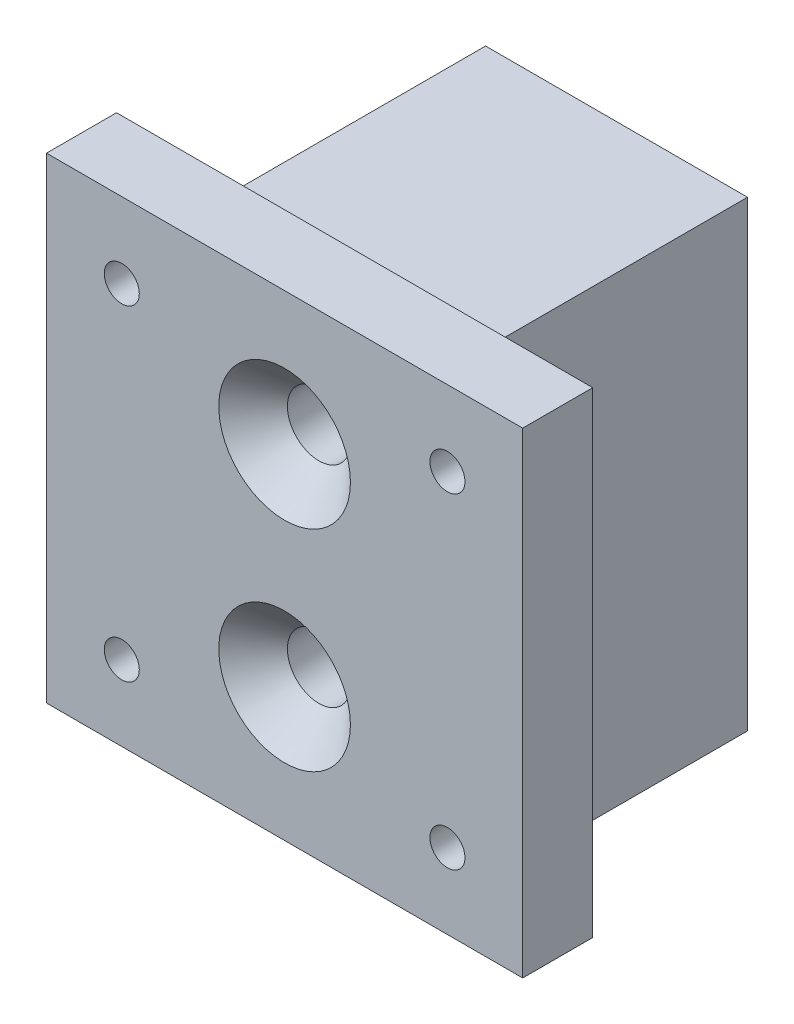
SolidWorks part; units mm, degrees
ref_plane "Front Plane" through (0, 0, 0) normal (0, 0, 1) x (1, 0, 0)
ref_plane "Top Plane" through (0, 0, 0) normal (0, 1, 0) x (1, 0, 0)
ref_plane "Right Plane" through (0, 0, 0) normal (1, 0, 0) x (0, 0, -1)
sketch "Sketch3" plane through (0, 0, 0) normal (0, 1, 0) x (1, 0, 0)
  line L1 (3, 3) -> (15.7, 3)
  line L2 (3, 3) -> (3, 15.7)
  line L3 (3, 15.7) -> (15.7, 15.7)
  line L4 (15.7, 3) -> (15.7, 15.7)
  line L5 (18.7, 18.7) -> (0, 18.7)
  line L6 (18.7, 18.7) -> (18.7, 0)
  line L7 (18.7, 0) -> (0, 0)
  line L8 (0, 18.7) -> (0, 0)
  dimension "D1" = 12.7
  dimension "D2" = 12.7
  dimension "D3" = 3
  dimension "D4" = 3
  dimension "D5" = 3
  dimension "D6" = 3
extrude "Boss-Extrude2" add sketch "Sketch3" along normal blind 30
sketch "Sketch4" plane through (0, 30, 0) normal (0, 1, 0) x (1, 0, 0)
  line L1 (0, 18.7) -> (18.7, 18.7)
  line L2 (0, 18.7) -> (0, 0)
  line L3 (0, 0) -> (18.7, 0)
  line L4 (18.7, 18.7) -> (18.7, 0)
extrude "Boss-Extrude3" add sketch "Sketch4" along normal blind 3
sketch "Sketch7" plane through (0, 0, 0) normal (0, 0, 1) x (1, 0, 0)
  line L1 (18.7, 33) -> (18.7, 0) construction
  line L2 (0, 33) -> (18.7, 33) construction
  point P0 (9.35, 24.9)
  point P1 (9.35, 9.9)
sketch "Sketch9" plane through (0, 0, 0) normal (0, 0, 1) x (1, 0, 0)
  line L0 (18.7, 33) -> (18.7, 0) construction
  line L1 (-7.65, 34.4) -> (26.35, 34.4)
  line L2 (-7.65, 34.4) -> (-7.65, 0.4)
  line L3 (-7.65, 0.4) -> (26.35, 0.4)
  line L4 (26.35, 34.4) -> (26.35, 0.4)
  point P4 (9.35, 17.4)
  point P5 (9.35, 17.4)
  dimension "D1" = 34
  dimension "D2" = 34
  dimension "D3" = 17
  dimension "D4" = 17
extrude "Boss-Extrude4" add sketch "Sketch9" along normal blind 5
sketch "Sketch10" plane through (0, 0, 5) normal (0, 0, 1) x (1, 0, 0)
  point P0 (9.35, 24.9)
  point P1 (9.35, 9.9)
hole_wizard "CSK for M4 Flat Head Machine Screw3" positions "3DSketch4" profile "Sketch11" countersink size "M4" standard "ANSI Metric" end condition through all
sketch3d "3DSketch4"
  point P0 (9.35, 24.9, 5)
  point P3 (9.35, 9.9, 5)
sketch "Sketch11" plane through (9.35, 24.9, 5) normal (1, 0, 0) x (0, -1, 0)
  line L0 (0, 0) -> (0, 23.7)
  line L1 (0, 23.7) -> (2.25, 23.7)
  line L2 (2.25, 23.7) -> (2.25, 2.45)
  line L3 (2.25, 2.45) -> (4.7, 0)
  line L5 (4.7, 0) -> (0, 0)
  line L6 (-2.25, 2.45) -> (-4.7, 0) construction
  line L11 (0, -6.35) -> (0, 107.95) construction
  dimension "Thru Hole Dia." = 4.5
  dimension "Thru Hole Depth" = 23.7
  dimension "Near C'Sink Dia." = 9.4
  dimension "Near C'Sink Angle" = 90
sketch "Sketch12" plane through (0, 0, 5) normal (0, 0, 1) x (1, 0, 0)
  line L0 (-7.65, 34.4) -> (-7.65, 0.4) construction
  line L1 (-2.275, 29.025) -> (20.975, 29.025)
  line L2 (-2.275, 29.025) -> (-2.275, 5.775)
  line L3 (-2.275, 5.775) -> (20.975, 5.775)
  line L4 (20.975, 29.025) -> (20.975, 5.775)
  point P4 (9.35, 17.4)
  point P5 (9.35, 17.4)
  dimension "D1" = 23.25
  dimension "D2" = 23.25
  dimension "D5" = 17
hole_wizard "Tap Drill for M3x0.5 Tap1" positions "3DSketch5" profile "Sketch13" hole size "M3x0.5" standard "ANSI Metric" end condition through all
sketch3d "3DSketch5"
  point P0 (-2.275, 29.025, 5)
  point P3 (20.975, 29.025, 5)
  point P6 (-2.275, 5.775, 5)
  point P9 (20.975, 5.775, 5)
sketch "Sketch13" plane through (-2.275, 29.025, 5) normal (1, 0, 0) x (0, -1, 0)
  line L0 (0, 0) -> (0, 23.7)
  line L1 (0, 23.7) -> (1.25, 23.7)
  line L2 (1.25, 23.7) -> (1.25, 0)
  line L5 (1.25, 0) -> (0, 0)
  line L11 (0, -6.35) -> (0, 107.95) construction
  dimension "Thru Hole Dia." = 2.5
  dimension "Thru Hole Depth" = 23.7
equation "\"wall_thickness\"= 3mm"
equation "\"loadcell\"= 12.7mm"
equation "\"D1@Sketch3\"=\"loadcell\""
equation "\"D2@Sketch3\"=\"loadcell\""
equation "\"D3@Sketch3\"=\"wall_thickness\""
equation "\"D4@Sketch3\"=\"wall_thickness\""
equation "\"D5@Sketch3\"=\"wall_thickness\""
equation "\"D6@Sketch3\"=\"wall_thickness\""
equation "\"D1@Boss-Extrude3\"=\"wall_thickness\""
equation "\"D3@Sketch7\"=0.0127/2+\"wall_thickness\""
equation "\"D4@Sketch7\"=0.0127/2+\"wall_thickness\""
equation "\"D1@Sketch7\"=0.0051+\"wall_thickness\""
equation "\"motormountsize\"= 34mm"
equation "\"D1@Sketch9\"=\"motormountsize\""
equation "\"D2@Sketch9\"=\"motormountsize\""
equation "\"D3@Sketch9\"=\"motormountsize\"/2"
equation "\"D4@Sketch9\"=\"motormountsize\"/2"
equation "\"D5@Sketch9\"=0.0127/2+\"wall_thickness\""
equation "\"D6@Sketch9\"=7.5mm"
equation "\"D1@Sketch12\"=23.25mm"
equation "\"D2@Sketch12\"=23.25mm"
equation "\"D3@Sketch12\"=11.625mm"
equation "\"D4@Sketch12\"=11.625mm"
